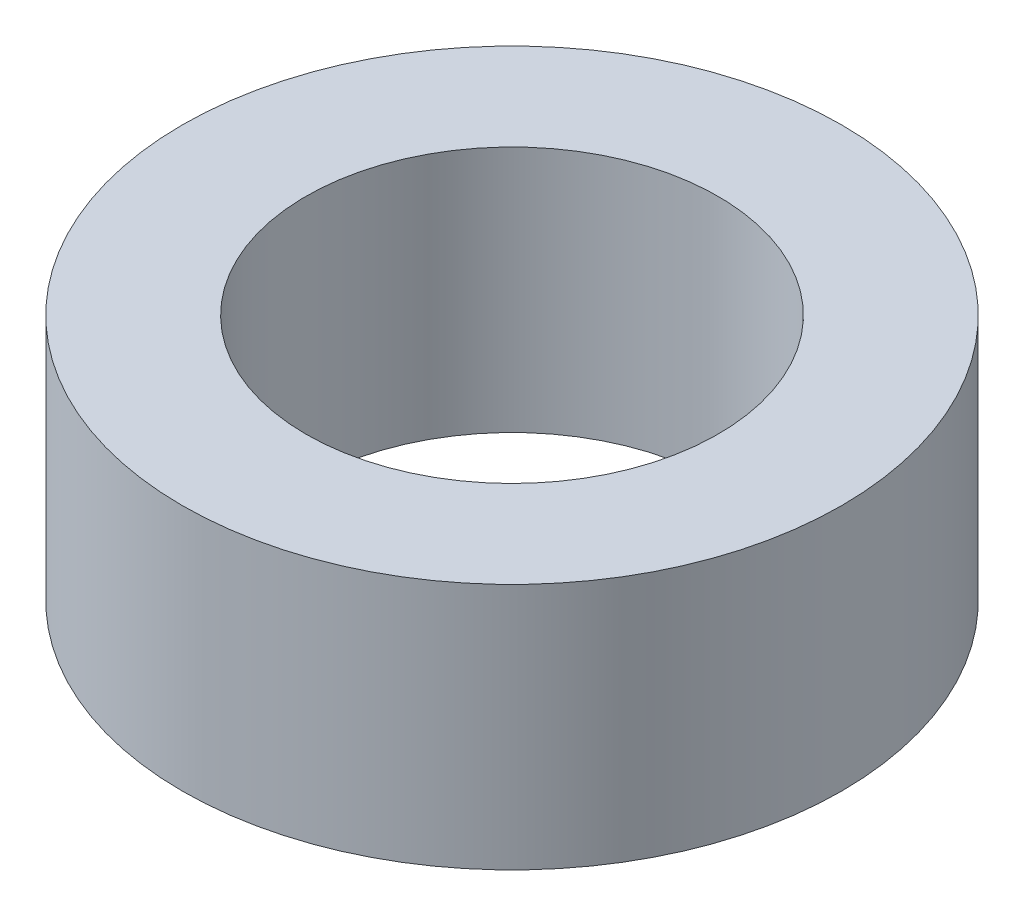
SolidWorks part; units mm, degrees
ref_plane "Front Plane" through (0, 0, 0) normal (0, 0, 1) x (1, 0, 0)
ref_plane "Top Plane" through (0, 0, 0) normal (0, 1, 0) x (1, 0, 0)
ref_plane "Right Plane" through (0, 0, 0) normal (1, 0, 0) x (0, 0, -1)
sketch "Sketch1" plane through (0, 0, 0) normal (0, 1, 0) x (1, 0, 0)
  circle A0 centre (0, 0) radius 2.5
  circle A1 centre (0, 0) radius 4
  dimension "D1" = 5
  dimension "D2" = 8
extrude "Boss-Extrude1" add sketch "Sketch1" along normal blind 3
